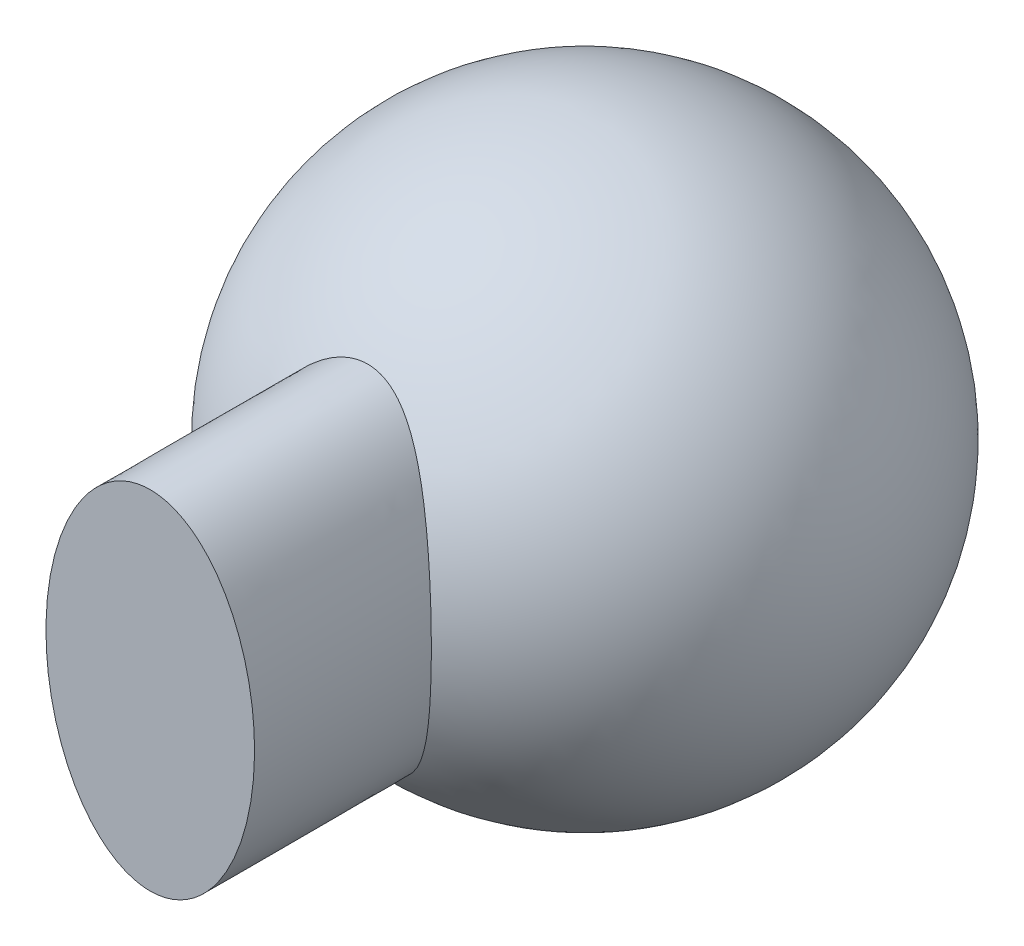
SolidWorks part; units mm, degrees
ref_plane "Front Plane" through (0, 0, 0) normal (0, 0, 1) x (1, 0, 0)
ref_plane "Top Plane" through (0, 0, 0) normal (0, 1, 0) x (1, 0, 0)
ref_plane "Right Plane" through (0, 0, 0) normal (1, 0, 0) x (0, 0, -1)
sketch "Sketch1" plane through (0, 0, 0) normal (0, 0, 1) x (1, 0, 0)
  line L0 (0, 12.7) -> (0, -12.7)
  arc A0 (0, 12.7) -> (0, -12.7) centre (0, 0) ccw
  dimension "D1" = 12.7
revolve "Revolve1" add sketch "Sketch1" angle 360 about L0
sketch "Sketch3" plane through (0, 0, 0) normal (0, 0, 1) x (1, 0, 0)
  ellipse E0 centre (0, 0) end of major axis (0, -7.9375) minor radius 4.7625
extrude "Boss-Extrude1" add sketch "Sketch3" along normal blind 19.8438
sketch "Sketch4" plane through (0, 0, 19.8438) normal (0, 0, 1) x (1, 0, 0)
  circle A0 centre (0, 0) radius 4.7625
